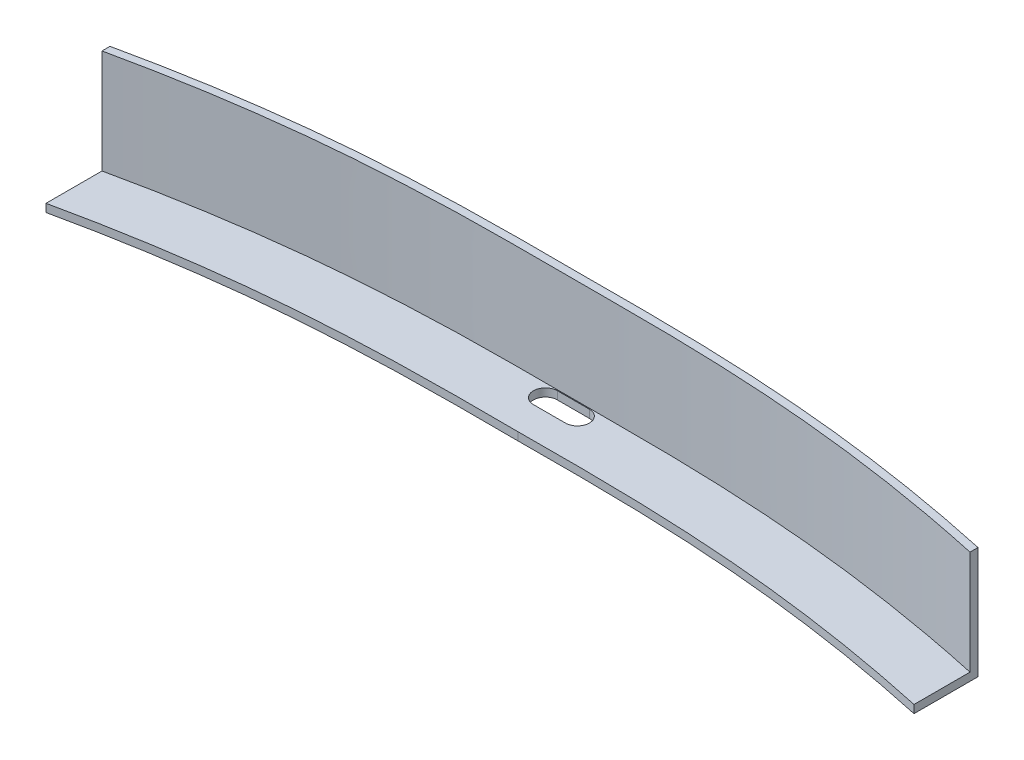
SolidWorks part; units mm, degrees
ref_plane "Front Plane" through (0, 0, 0) normal (0, 0, 1) x (1, 0, 0)
ref_plane "Top Plane" through (0, 0, 0) normal (0, 1, 0) x (1, 0, 0)
ref_plane "Right Plane" through (0, 0, 0) normal (1, 0, 0) x (0, 0, -1)
sketch "Sketch1" plane through (0, 0, 0) normal (0, 1, 0) x (1, 0, 0)
  line L0 (189.6667, 320) -> (948.3333, 320) construction
  line L1 (-903.6669, 221.9416) -> (-806.6741, 223.1267) construction
  line L2 (-2.4415, 6.8053) -> (-2.4415, 30.0052) construction
  line L3 (-115.408, 6.8053) -> (110.5249, 6.8053)
  line L4 (-115.408, 6.8053) -> (-115.408, -50.1579)
  line L5 (-115.408, -50.1579) -> (110.5249, -50.1579)
  line L6 (110.5249, 6.8053) -> (110.5249, -50.1579)
  line L7 (-2.4415, 6.8053) -> (-2.4415, -2.9496) construction
  line L8 (-56.7109, 8.0428) -> (-56.7109, -1.9572)
  line L9 (51.8279, 8.0428) -> (51.8279, -1.9572)
  line L10 (-56.7109, 10.0428) -> (-56.7109, -3.9572)
  line L11 (51.8279, -3.9572) -> (51.8279, 10.0428)
  spline S0 degree 3 poles (-56.7109, 8.0428) (-48.3237, 9.8705) (-35.0274, 11.9379) (-16.8793, 12.8603) (-7.6058, 12.8449) (-2.4415, 12.8177) knots 0 0 0 0 0.472031 0.735861 1 1 1 1
  spline S1 degree 3 poles (-56.7109, -1.9572) (-48.3237, -0.1295) (-35.0274, 1.9379) (-16.8793, 2.8603) (-7.6058, 2.8449) (-2.4415, 2.8177) knots 0 0 0 0 0.472031 0.735861 1 1 1 1
  spline S2 degree 3 poles (51.8279, -1.9572) (43.4407, -0.1295) (30.1443, 1.9379) (11.9963, 2.8603) (2.7228, 2.8449) (-2.4415, 2.8177) knots 0 0 0 0 0.472031 0.735861 1 1 1 1
  spline S3 degree 3 poles (51.8279, 8.0428) (43.4407, 9.8705) (30.1443, 11.9379) (11.9963, 12.8603) (2.7228, 12.8449) (-2.4415, 12.8177) knots 0 0 0 0 0.472031 0.735861 1 1 1 1
  spline S4 degree 3 poles (-56.7109, 10.0428) (-48.3237, 11.8705) (-35.0274, 13.9379) (-16.8793, 14.8603) (-7.6058, 14.8449) (-2.4415, 14.8177) knots 0 0 0 0 0.472031 0.735861 1 1 1 1
  spline S5 degree 3 poles (51.8279, 10.0428) (43.4407, 11.8705) (30.1443, 13.9379) (11.9963, 14.8603) (2.7228, 14.8449) (-2.4415, 14.8177) knots 0 0 0 0 0.472031 0.735861 1 1 1 1
  spline S6 degree 3 poles (-56.7109, -3.9572) (-48.3237, -2.1295) (-35.0274, -0.0621) (-16.8793, 0.8603) (-7.6058, 0.8449) (-2.4415, 0.8177) knots 0 0 0 0 0.472031 0.735861 1 1 1 1
  spline S7 degree 3 poles (51.8279, -3.9572) (43.4407, -2.1295) (30.1443, -0.0621) (11.9963, 0.8603) (2.7228, 0.8449) (-2.4415, 0.8177) knots 0 0 0 0 0.472031 0.735861 1 1 1 1
  spline S8 degree 3 poles (-56.7109, 3.0428) (-48.3237, 4.8705) (-35.0274, 6.9379) (-16.8793, 7.8603) (-7.6058, 7.8449) (-2.4415, 7.8177) knots 0 0 0 0 0.472031 0.735861 1 1 1 1
  spline S9 degree 3 poles (51.8279, 3.0428) (43.4407, 4.8705) (30.1443, 6.9379) (11.9963, 7.8603) (2.7228, 7.8449) (-2.4415, 7.8177) knots 0 0 0 0 0.472031 0.735861 1 1 1 1
  spline S10 degree 3 poles (-56.7109, 2.0428) (-48.3237, 3.8705) (-35.0274, 5.9379) (-16.8793, 6.8603) (-7.6058, 6.8449) (-2.4415, 6.8177) knots 0 0 0 0 0.472031 0.735861 1 1 1 1
  spline S11 degree 3 poles (51.8279, 2.0428) (43.4407, 3.8705) (30.1443, 5.9379) (11.9963, 6.8603) (2.7228, 6.8449) (-2.4415, 6.8177) knots 0 0 0 0 0.472031 0.735861 1 1 1 1
  point P30 (-56.7109, 3.0428)
  dimension "D2" = 7
  dimension "D1" = 97
extrude "Boss-Extrude1" add sketch "Sketch1" along normal blind 14 contours L10 S10 L3 S8 | S11 L3 S9 S8 S10 | S11 L11 S9 L3 | S9 L3 L9 S3 S0 L8 S8 | L8 S8 L3 | S9 L9 L3 | L11 S5 S4 L10 S0 S3
sketch "Sketch2" plane through (0, 14, 0) normal (0, 1, 0) x (1, 0, 0)
  line L0 (-54.7109, 5.9684) -> (-54.7109, 16.468)
  line L1 (-56.7109, 10.0428) -> (-56.7109, 2.0428) construction
  line L2 (-2.4415, 14.8177) -> (-2.4415, 22.16) construction
  line L3 (49.8279, 5.9684) -> (49.8279, 19.3538)
  line L4 (51.8279, 2.0428) -> (51.8279, 10.0428) construction
  line L5 (-54.7109, 16.468) -> (49.8279, 19.3538)
  line L7 (-60.8022, 3.8953) -> (-51.2181, -5.3938)
  line L8 (-51.2181, -5.3938) -> (49.0947, -7.2615)
  line L9 (49.0947, -7.2615) -> (58.1658, 3.0428)
  line L11 (-56.7109, 9.0428) -> (-60.8022, 3.8953)
  line L12 (51.8279, 9.0428) -> (58.1658, 3.0428)
  spline S1 degree 3 poles (-56.7109, 9.0428) (-51.0153, 10.2834) (-42.2215, 11.8261) (-30.4783, 13.0862) (-21.9608, 13.606) (-12.6803, 13.8661) (-2.4883, 13.7888) (7.8396, 13.8667) (17.1432, 13.6046) (25.5947, 13.0817) (37.2496, 11.8392) (46.0225, 10.3073) (51.8279, 9.0428) knots 0 0 0 0 0.160114 0.245012 0.324303 0.394459 0.5 0.604256 0.678146 0.755619 0.836799 1 1 1 1
  spline S3 degree 3 poles (-56.7109, 5.5428) (-51.0153, 6.7834) (-42.2215, 8.3261) (-30.4783, 9.5862) (-21.9608, 10.106) (-12.6803, 10.3661) (-2.4883, 10.2888) (7.8396, 10.3667) (17.1432, 10.1046) (25.5947, 9.5817) (37.2496, 8.3392) (46.0225, 6.8073) (51.8279, 5.5428) knots 0 0 0 0 0.160114 0.245012 0.324303 0.394459 0.5 0.604256 0.678146 0.755619 0.836799 1 1 1 1
  dimension "D1" = 2
  dimension "D2" = 2
extrude "Cut-Extrude1" cut sketch "Sketch2" against normal blind 13
sketch "Sketch7" plane through (0, 1, 0) normal (0, 1, 0) x (1, 0, 0)
  line L0 (-4.4415, 12.2177) -> (-0.4415, 12.2177) construction
  line L1 (-4.4415, 13.7177) -> (-0.4415, 13.7177)
  line L2 (-4.4415, 10.7177) -> (-0.4415, 10.7177)
  arc A1 (-4.4415, 13.7177) -> (-4.4415, 10.7177) centre (-4.4415, 12.2177) ccw
  arc A2 (-0.4415, 10.7177) -> (-0.4415, 13.7177) centre (-0.4415, 12.2177) ccw
  point P2 (-2.4415, 12.2177)
  dimension "D1" = 0
  dimension "D2" = 5.4
  dimension "D3" = 1.5
  dimension "D4" = 4
extrude "Cut-Extrude4" cut sketch "Sketch7" against normal blind 10 and the other way blind 8
